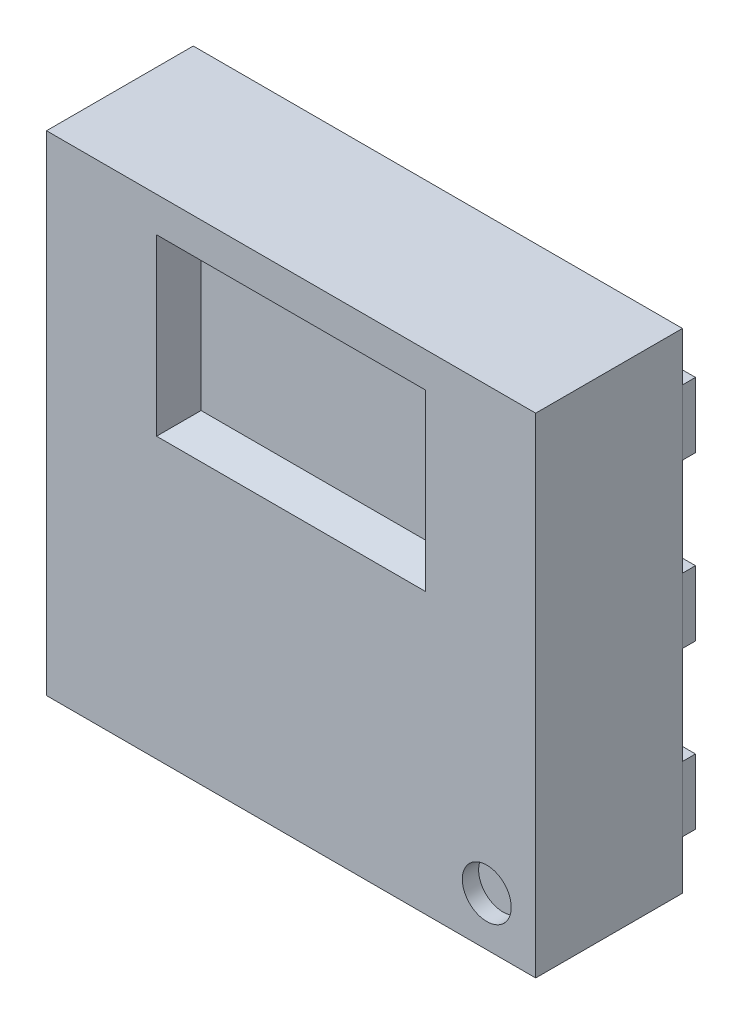
SolidWorks part; units mm, degrees
ref_plane "Front Plane" through (0, 0, 0) normal (0, 0, 1) x (1, 0, 0)
ref_plane "Top Plane" through (0, 0, 0) normal (0, 1, 0) x (1, 0, 0)
ref_plane "Right Plane" through (0, 0, 0) normal (1, 0, 0) x (0, 0, -1)
sketch "Sketch1" plane through (0, 0, 0) normal (0, 0, 1) x (1, 0, 0)
  line L1 (0, 0) -> (3, 0)
  line L2 (0, 0) -> (0, 3)
  line L3 (0, 3) -> (3, 3)
  line L4 (3, 0) -> (3, 3)
  dimension "D1" = 3
  dimension "D2" = 3
extrude "Boss-Extrude1" add sketch "Sketch1" along normal blind 0.9
sketch "Sketch2" plane through (0, 0, 0.9) normal (0, 0, 1) x (1, 0, 0)
  line L0 (3, 3) -> (0, 3) construction
  line L1 (0.675, 2.785) -> (2.325, 2.785)
  line L2 (0.675, 2.785) -> (0.675, 1.715)
  line L3 (0.675, 1.715) -> (2.325, 1.715)
  line L4 (2.325, 2.785) -> (2.325, 1.715)
  line L5 (3, 0) -> (3, 3) construction
  dimension "D1" = 1.65
  dimension "D2" = 1.07
  dimension "D3" = 0.215
  dimension "D4" = 0.675
extrude "Cut-Extrude1" cut sketch "Sketch2" against normal blind 0.2 draft 20
sketch "Sketch3" plane through (0, 0, 0) normal (0, 0, -1) x (-1, 0, 0)
  line L0 (-1.5, 3) -> (-1.5, 0) construction
  line L1 (-3, 3) -> (0, 3) construction
  line L2 (0, 0) -> (-3, 0) construction
  line L3 (-2.25, 0.5828) -> (-1.9672, 0.3)
  line L4 (-3, 0) -> (-3, 3) construction
  line L5 (-3, 1.5) -> (0, 1.5) construction
  line L6 (0, 3) -> (0, 0) construction
  line L7 (-2.25, 2.7) -> (-0.75, 2.7)
  line L8 (-2.25, 2.7) -> (-2.25, 0.5828)
  line L9 (-1.9672, 0.3) -> (-0.75, 0.3)
  line L10 (-0.75, 2.7) -> (-0.75, 0.3)
  point P16 (-0.75, 1.5)
  point P17 (-1.5, 2.7)
  dimension "D1" = 1.5
  dimension "D2" = 2.4
  dimension "D3" = 45
  dimension "D4" = 0.4
extrude "Boss-Extrude2" add sketch "Sketch3" along normal blind 0.08
sketch "Sketch4" plane through (0, 0, 0) normal (0, 0, -1) x (-1, 0, 0)
  line L0 (-3, 0) -> (-3, 3) construction
  line L1 (-3, 0.3) -> (-2.6, 0.3)
  line L2 (-3, 0.3) -> (-3, 0.7)
  line L3 (-3, 0.7) -> (-2.6, 0.7)
  line L4 (-2.6, 0.3) -> (-2.6, 0.7)
  line L5 (-3, 1.5) -> (0, 1.5) construction
  line L6 (0, 3) -> (0, 0) construction
  line L7 (-3, 0.5) -> (-2.6, 0.5) construction
  line L8 (-1.9672, 0.3) -> (-0.75, 0.3) construction
  line L9 (-3, 1.3) -> (-2.6, 1.3)
  line L10 (-3, 1.3) -> (-3, 1.7)
  line L11 (-3, 1.7) -> (-2.6, 1.7)
  line L12 (-2.6, 1.3) -> (-2.6, 1.7)
  line L13 (-3, 1.5) -> (-2.6, 1.5) construction
  line L14 (-3, 2.3) -> (-2.6, 2.3)
  line L15 (-3, 2.3) -> (-3, 2.7)
  line L16 (-3, 2.7) -> (-2.6, 2.7)
  line L17 (-2.6, 2.3) -> (-2.6, 2.7)
  line L18 (-3, 2.5) -> (-2.6, 2.5) construction
  line L19 (-1.5, 3) -> (-1.5, 0) construction
  line L20 (-3, 3) -> (0, 3) construction
  line L21 (0, 0) -> (-3, 0) construction
  line L22 (0, 2.5) -> (-0.4, 2.5) construction
  line L23 (0, 1.5) -> (-0.4, 1.5) construction
  line L24 (0, 0.5) -> (-0.4, 0.5) construction
  line L25 (-0.4, 2.3) -> (-0.4, 2.7)
  line L26 (0, 2.7) -> (-0.4, 2.7)
  line L27 (0, 2.3) -> (0, 2.7)
  line L28 (0, 2.3) -> (-0.4, 2.3)
  line L29 (-0.4, 1.3) -> (-0.4, 1.7)
  line L30 (0, 1.7) -> (-0.4, 1.7)
  line L31 (0, 1.3) -> (0, 1.7)
  line L32 (0, 1.3) -> (-0.4, 1.3)
  line L33 (-0.4, 0.3) -> (-0.4, 0.7)
  line L34 (0, 0.7) -> (-0.4, 0.7)
  line L35 (0, 0.3) -> (0, 0.7)
  line L36 (0, 0.3) -> (-0.4, 0.3)
  dimension "D1" = 0.4
  dimension "D2" = 0.4
  dimension "D3" = 3
extrude "Boss-Extrude3" add sketch "Sketch4" along normal blind 0.08 separate body
sketch "Sketch5" plane through (0, 0, 0.9) normal (0, 0, 1) x (1, 0, 0)
  line L0 (3, 0) -> (3, 3) construction
  line L1 (0, 0) -> (3, 0) construction
  circle A0 centre (2.7, 0.3) radius 0.15
  dimension "D3" = 0.3
  dimension "D1" = 0.3
  dimension "D2" = 0.3
extrude "Cut-Extrude2" cut sketch "Sketch5" against normal blind 0.1
